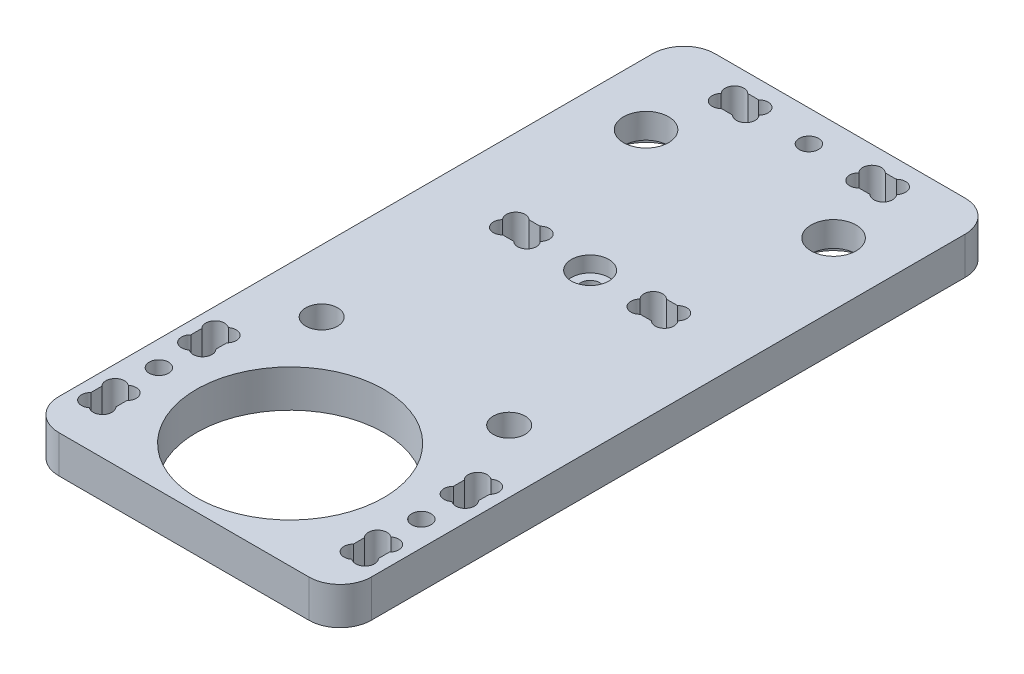
SolidWorks part; units mm, degrees
ref_plane "Alzado" through (0, 0, 0) normal (0, 0, 1) x (1, 0, 0)
ref_plane "Planta" through (0, 0, 0) normal (0, 1, 0) x (1, 0, 0)
ref_plane "Vista lateral" through (0, 0, 0) normal (1, 0, 0) x (0, 0, -1)
sketch "Croquis1" plane through (0, 0, 0) normal (0, 1, 0) x (1, 0, 0)
  line L0 (0, -36.0891) -> (0, 0) construction
  line L1 (-25, -52.5) -> (25, -52.5)
  line L2 (-25, -52.5) -> (-25, 52.5)
  line L3 (-25, 52.5) -> (25, 52.5)
  line L4 (25, -52.5) -> (25, 52.5)
  line L5 (-25, -52.5) -> (25, 52.5) construction
  line L6 (-25, 52.5) -> (25, -52.5) construction
  point P0 (0, 0)
  dimension "D2" = 50
  dimension "D1" = 105
extrude "Saliente-Extruir1" add sketch "Croquis1" along normal blind 6
sketch "Croquis2" plane through (0, 6, 0) normal (0, 1, 0) x (1, 0, 0)
  line L0 (0, 10.5) -> (0, 52.5) construction
  line L1 (-15, -15.45) -> (15, -15.45) construction
  line L2 (-15, -15.45) -> (-15, 36.45) construction
  line L3 (-15, 36.45) -> (15, 36.45) construction
  line L4 (15, -15.45) -> (15, 36.45) construction
  line L5 (-15, -15.45) -> (15, 36.45) construction
  line L6 (-15, 36.45) -> (15, -15.45) construction
  line L7 (25, 52.5) -> (-25, 52.5) construction
  circle A0 centre (-15, 36.45) radius 3.6
  circle A1 centre (15, 36.45) radius 3.6
  circle A2 centre (15, -15.45) radius 2.55
  circle A3 centre (-15, -15.45) radius 2.55
  point P0 (0, 10.5)
  dimension "D3" = 7.2
  dimension "D5" = 5.1
  dimension "D1" = 30
  dimension "D2" = 51.9
  dimension "D4" = 42
extrude "Cortar-Extruir2" cut sketch "Croquis2" against normal through all
sketch "Croquis4" plane through (0, 0, 0) normal (0, -1, 0) x (1, 0, 0)
  circle A0 centre (15, -36.45) radius 6
  circle A1 centre (-15, -36.45) radius 6
  circle A2 centre (-15, 15.45) radius 5.05
  circle A3 centre (15, 15.45) radius 5.05
  dimension "D1" = 12
  dimension "D2" = 10.1
extrude "Cortar-Extruir3" cut sketch "Croquis4" against normal blind 2
sketch "Croquis5" plane through (0, 6, 0) normal (0, 1, 0) x (1, 0, 0)
  line L1 (-25, 49.6) -> (25, 49.6) construction
  line L2 (-25, 49.6) -> (-25, 45.4) construction
  line L3 (-25, 45.4) -> (25, 45.4) construction
  line L4 (25, 49.6) -> (25, 45.4) construction
  line L5 (-25, 52.5) -> (-25, -52.5) construction
  line L6 (25, -52.5) -> (25, 52.5) construction
  line L7 (25, 52.5) -> (-25, 52.5) construction
  line L8 (-11, 49.6) -> (-11, 45.4) construction
  line L9 (-14, 49.6) -> (-8, 49.6)
  line L10 (-14, 49.6) -> (-14, 45.4)
  line L11 (-14, 45.4) -> (-8, 45.4)
  line L12 (-8, 49.6) -> (-8, 45.4)
  line L13 (8, 49.6) -> (14, 49.6)
  line L14 (8, 49.6) -> (8, 45.4)
  line L15 (8, 45.4) -> (14, 45.4)
  line L16 (14, 49.6) -> (14, 45.4)
  line L17 (11, 49.6) -> (11, 45.4) construction
  line L18 (-11, 47.5) -> (-25, 47.5) construction
  line L19 (11, 47.5) -> (25, 47.5) construction
  line L20 (0, 49.6) -> (0, 45.4) construction
  circle A0 centre (0, 47.5) radius 1.55
  dimension "D5" = 3.1
  dimension "D1" = 4.2
  dimension "D2" = 2.9
  dimension "D3" = 6
  dimension "D4" = 14
extrude "Cortar-Extruir4" cut sketch "Croquis5" against normal through all
ref_plane "Plano1" through (0, 0, -47.5) normal (0, 0, 1) x (1, 0, 0)
ref_plane "Plano2" through (0, 0, -12.5) normal (0, 0, -1) x (-1, 0, 0)
ref_plane "Plano3" through (0, 0, -30) normal (0, 0, 1) x (1, 0, 0)
ref_plane "Plano5" through (0, 3, 0) normal (0, -1, 0) x (-1, 0, 0)
sketch "Croquis8" plane through (0, 6, 0) normal (0, 1, 0) x (1, 0, 0)
  line L0 (0, 47.5) -> (0, 51.5203) construction
  line L1 (-11.8787, 49.6) -> (-10.1213, 49.6)
  line L2 (-8, 49.6) -> (-14, 49.6) construction
  line L3 (-10.1213, 45.4) -> (-11.8787, 45.4)
  line L4 (-14, 49.6) -> (-14, 45.4) construction
  line L5 (-14, 49.6) -> (-12.5, 48.1) construction
  line L6 (-14, 45.4) -> (-8, 45.4) construction
  line L7 (14, 49.6) -> (12.5, 48.1) construction
  line L8 (10.1213, 45.4) -> (11.8787, 45.4)
  line L9 (11.8787, 49.6) -> (10.1213, 49.6)
  arc A0 (-11.8787, 49.6) -> (-14.0209, 47.5) centre (-12.9393, 48.5393) ccw
  arc A1 (-7.9791, 47.5) -> (-10.1213, 49.6) centre (-9.0607, 48.5393) ccw
  arc A2 (-10.1213, 45.4) -> (-7.9791, 47.5) centre (-9.0607, 46.4607) ccw
  arc A3 (-14.0209, 47.5) -> (-11.8787, 45.4) centre (-12.9393, 46.4607) ccw
  circle A4 centre (-12.5, 48.1) radius 1.5 construction
  circle A5 centre (12.5, 48.1) radius 1.5 construction
  arc A6 (14.0209, 47.5) -> (11.8787, 45.4) centre (12.9393, 46.4607) cw
  arc A7 (10.1213, 45.4) -> (7.9791, 47.5) centre (9.0607, 46.4607) cw
  arc A8 (7.9791, 47.5) -> (10.1213, 49.6) centre (9.0607, 48.5393) cw
  arc A9 (11.8787, 49.6) -> (14.0209, 47.5) centre (12.9393, 48.5393) cw
  dimension "D1" = 3
extrude "Cortar-Extruir6" cut sketch "Croquis8" against normal through all
mirror "Simetría1" about plane through (0, 0, -30) normal (0, 0, 1) of "Cortar-Extruir6", "Cortar-Extruir4"
sketch "Croquis14" plane through (0, 6, 0) normal (0, 1, 0) x (1, 0, 0)
  circle A0 centre (0, 12.5) radius 3
  dimension "D1" = 6
extrude "Cortar-Extruir9" cut sketch "Croquis14" against normal blind 2.5
sketch "Croquis16" plane through (0, 0, 0) normal (0, -1, 0) x (1, 0, 0)
  line L0 (0, 0) -> (0, 35.5) construction
  circle A0 centre (0, 35.5) radius 15
  dimension "D1" = 30
  dimension "D2" = 35.5
extrude "Cortar-Extruir10" cut sketch "Croquis16" against normal through all
sketch "Croquis17" plane through (0, 6, 0) normal (0, 1, 0) x (1, 0, 0)
  line L0 (-23, -24.5) -> (-19, -30.5) construction
  line L1 (-21, -27.5) -> (-21, -35.5) construction
  line L2 (-21, -35.5) -> (-10.7672, -35.5) construction
  line L3 (-23, -40.5) -> (-23, -46.5)
  line L4 (-23, -46.5) -> (-19, -46.5)
  line L5 (-19, -46.5) -> (-19, -40.5)
  line L6 (-19, -40.5) -> (-23, -40.5)
  line L7 (19, -46.5) -> (19, -40.5)
  line L16 (0, 0) -> (0, -46.5043) construction
  line L17 (23, -46.5) -> (19, -46.5)
  line L18 (23, -40.5) -> (23, -46.5)
  line L19 (19, -40.5) -> (23, -40.5)
  line L20 (23, -24.5) -> (19, -24.5)
  line L21 (23, -30.5) -> (23, -24.5)
  line L22 (19, -30.5) -> (23, -30.5)
  line L23 (19, -24.5) -> (19, -30.5)
  line L37 (-19, -24.5) -> (-19, -30.5)
  line L38 (-23, -24.5) -> (-19, -24.5)
  line L39 (-23, -30.5) -> (-23, -24.5)
  line L40 (-19, -30.5) -> (-23, -30.5)
  circle A1 centre (-21, -35.5) radius 1.55 construction
  circle A2 centre (21, -35.5) radius 1.55
  circle A3 centre (-21, -35.5) radius 1.55
  dimension "D1" = 6
  dimension "D2" = 4
  dimension "D3" = 8
extrude "Cortar-Extruir11" cut sketch "Croquis17" against normal through all
fillet "Redondeo1" radius 5 4 edges at (-25, 3, -52.5) (25, 3, -52.5) (-25, 3, 52.5) (25, 3, 52.5)
sketch "Croquis18" plane through (0, 6, 0) normal (0, 1, 0) x (1, 0, 0)
  line L0 (-19, -24.5) -> (-23, -24.5) construction
  line L1 (-23, -24.5) -> (-23, -30.5) construction
  line L2 (-23, -24.5) -> (-21.5, -26) construction
  line L3 (-21, -30.5) -> (-21, -27.7627) construction
  line L4 (-23, -30.5) -> (-19, -30.5) construction
  line L5 (-19, -27.5) -> (-16.1344, -27.5) construction
  line L6 (-19, -30.5) -> (-19, -24.5) construction
  line L7 (-21, -35.5) -> (0, -35.5) construction
  line L8 (0, -35.5) -> (0, 0) construction
  circle A0 centre (-21.5, -26) radius 1.5 construction
  arc A1 (-21, -24.3912) -> (-21, -26.7301) centre (-21.9393, -25.5607) ccw
  arc A2 (-21, -24.3912) -> (-21, -26.7301) centre (-20.0607, -25.5607) cw
  arc A3 (-21, -30.6088) -> (-21, -28.2699) centre (-21.9393, -29.4393) cw
  arc A4 (-21, -30.6088) -> (-21, -28.2699) centre (-20.0607, -29.4393) ccw
  arc A5 (-21, -46.6088) -> (-21, -44.2699) centre (-20.0607, -45.4393) ccw
  arc A6 (-21, -46.6088) -> (-21, -44.2699) centre (-21.9393, -45.4393) cw
  arc A7 (-21, -40.3912) -> (-21, -42.7301) centre (-21.9393, -41.5607) ccw
  arc A8 (-21, -40.3912) -> (-21, -42.7301) centre (-20.0607, -41.5607) cw
  arc A9 (21, -24.3912) -> (21, -26.7301) centre (20.0607, -25.5607) ccw
  arc A10 (21, -24.3912) -> (21, -26.7301) centre (21.9393, -25.5607) cw
  arc A11 (21, -30.6088) -> (21, -28.2699) centre (20.0607, -29.4393) cw
  arc A12 (21, -30.6088) -> (21, -28.2699) centre (21.9393, -29.4393) ccw
  arc A13 (21, -40.3912) -> (21, -42.7301) centre (20.0607, -41.5607) ccw
  arc A14 (21, -40.3912) -> (21, -42.7301) centre (21.9393, -41.5607) cw
  arc A15 (21, -46.6088) -> (21, -44.2699) centre (21.9393, -45.4393) ccw
  arc A16 (21, -46.6088) -> (21, -44.2699) centre (20.0607, -45.4393) cw
  dimension "D1" = 3
extrude "Cortar-Extruir12" cut sketch "Croquis18" against normal through all
